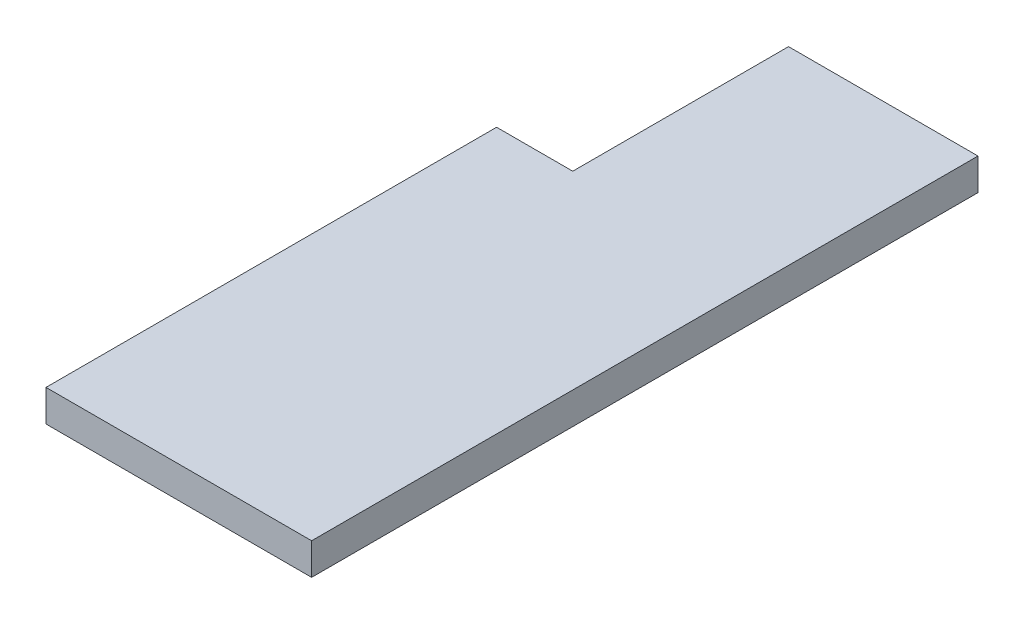
SolidWorks part; units mm, degrees
ref_plane "Front Plane" through (0, 0, 0) normal (0, 0, 1) x (1, 0, 0)
ref_plane "Top Plane" through (0, 0, 0) normal (0, 1, 0) x (1, 0, 0)
ref_plane "Right Plane" through (0, 0, 0) normal (1, 0, 0) x (0, 0, -1)
sketch "Sketch1" plane through (0, 0, 0) normal (0, 1, 0) x (1, 0, 0)
  line L1 (0, 0) -> (-53.594, 0)
  line L2 (0, 0) -> (0, 82.55)
  line L3 (0, 82.55) -> (-53.594, 82.55)
  line L4 (-53.594, 0) -> (-53.594, 82.55)
  dimension "D1" = 82.55
  dimension "D2" = 53.594
extrude "Boss-Extrude1" add sketch "Sketch1" along normal blind 6.35
sketch "Sketch6" plane through (0, 0, 0) normal (0, 0, 1) x (1, 0, 0)
  line L1 (0, 6.35) -> (-53.594, 6.35)
  line L2 (0, 6.35) -> (0, 0)
  line L3 (0, 0) -> (-53.594, 0)
  line L4 (-53.594, 6.35) -> (-53.594, 0)
extrude "Boss-Extrude3" add sketch "Sketch6" along normal blind 7.62
ref_plane "KORAL!!!" through (-26.797, 0, 0) normal (1, 0, 0) x (0, 0, -1)
sketch "Sketch3" plane through (0, 6.35, 0) normal (0, 1, 0) x (1, 0, 0)
  line L1 (0, 82.55) -> (0, -7.62)
  line L2 (-0.508, -7.62) -> (-0.508, 82.55)
  line L3 (0, 82.55) -> (-53.594, 82.55) construction
  line L4 (-0.508, 82.55) -> (0, 82.55)
  line L6 (0, -7.62) -> (-53.594, -7.62) construction
  line L7 (0, -7.62) -> (-0.508, -7.62)
  dimension "D1" = 0.508
extrude "Cut-Extrude2" cut sketch "Sketch3" against normal up to next (6.35 mm away)
mirror "Mirror1" about plane through (-26.797, 0, 0) normal (1, 0, 0) of "Cut-Extrude2"
sketch "Sketch8" plane through (0, 0, -82.55) normal (0, 0, -1) x (-1, 0, 0)
  line L0 (0.508, 0) -> (53.086, 0) construction
  line L1 (0.508, 6.35) -> (37.846, 6.35)
  line L2 (0.508, 6.35) -> (0.508, 0)
  line L3 (0.508, 0) -> (37.846, 0)
  line L4 (37.846, 6.35) -> (37.846, 0)
  line L5 (53.086, 0) -> (53.086, 6.35) construction
  dimension "D1" = 15.24
extrude "Boss-Extrude4" add sketch "Sketch8" along normal blind 43.18
sketch "Sketch9" plane through (0, 0, 0) normal (0, 0, 1) x (1, 0, 0)
  line L0 (7.4165, 3.5859) -> (-19.1601, 49.6179) construction
  line L1 (-19.1601, 49.6179) -> (-33.0389, 49.6179) construction
  line L2 (-33.0389, 49.6179) -> (-59.3747, 3.4478) construction
  line L3 (-59.3747, 3.4478) -> (-53.086, 0) construction
  line L5 (1.2055, 0) -> (7.4165, 3.5859) construction
  line L7 (-53.086, 0) -> (1.2055, 0) construction
  line L10 (-53.086, 6.35) -> (0.0672, 6.35)
  line L11 (-53.086, 6.35) -> (-53.086, 0)
  line L12 (-53.086, 0) -> (0.0672, 0)
  line L13 (0.0672, 6.35) -> (0.0672, 0)
  dimension "D1" = 53.1532
  dimension "D2" = 13.8788
  dimension "D3" = 1.2055
  dimension "D4" = 7.4165
  dimension "D5" = 19.1601
sketch "Sketch10" plane through (0, 0, 7.62) normal (0, 0, 1) x (1, 0, 0)
  line L0 (-33.0389, 49.6179) -> (-59.3747, 3.4478) construction
  line L5 (-53.086, 0) -> (0.0672, 0)
  line L6 (-53.086, 0) -> (-53.086, 6.35)
  line L7 (-53.086, 6.35) -> (0.0672, 6.35)
  line L8 (0.0672, 0) -> (0.0672, 6.35)
  line L9 (-53.086, 6.35) -> (0.0672, 6.35) construction
extrude "Boss-Extrude5" add sketch "Sketch10" against normal up to surface (90.17 mm away) up to face at (-45.466, 3.175, -82.55)
sketch "Sketch11" plane through (0, 0, -82.55) normal (0, 0, -1) x (-1, 0, 0)
  line L1 (-0.0672, 6.35) -> (0.508, 6.35)
  line L2 (-0.0672, 6.35) -> (-0.0672, 0)
  line L3 (-0.0672, 0) -> (0.508, 0)
  line L4 (0.508, 6.35) -> (0.508, 0)
extrude "Boss-Extrude6" add sketch "Sketch11" along normal up to surface (43.18 mm away) up to face at (-19.177, 3.175, -125.73)
sketch "Sketch12" plane through (0, 6.35, 6.35) normal (0, 1, 0) x (1, 0, 0)
  line L0 (-49.276, 2.54) -> (-49.276, 78.74) construction
  line L1 (-49.276, 78.74) -> (-3.7744, 78.74) construction
  line L2 (-3.7744, 78.74) -> (-3.7744, 2.54) construction
  line L3 (-3.7744, 2.54) -> (-49.276, 2.54) construction
  line L4 (-49.276, 78.74) -> (-53.086, 78.74) construction
  line L5 (-53.086, 78.74) -> (-53.086, 88.9) construction
  line L6 (0.0672, 132.08) -> (0.0672, -1.27) construction
  line L7 (-37.846, 132.08) -> (0.0672, 132.08) construction
  circle A0 centre (-49.276, 2.54) radius 1.905
  circle A1 centre (-49.276, 78.74) radius 1.905
  circle A2 centre (-3.7744, 78.74) radius 1.905
  circle A3 centre (-3.7744, 2.54) radius 1.905
  dimension "D1" = 3.81
  dimension "D2" = 3.8416
  dimension "D3" = 49.3432
  dimension "D4" = 53.34
  dimension "D5" = 129.54
